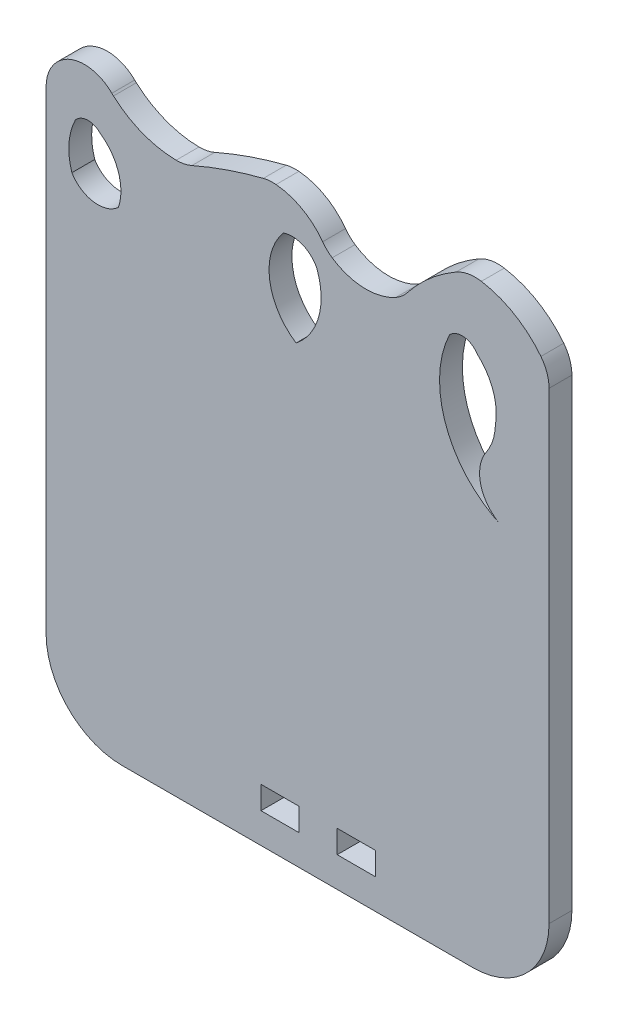
SolidWorks part; units mm, degrees
ref_plane "Alzado" through (0, 0, 0) normal (0, 0, 1) x (1, 0, 0)
ref_plane "Planta" through (0, 0, 0) normal (0, 1, 0) x (1, 0, 0)
ref_plane "Vista lateral" through (0, 0, 0) normal (1, 0, 0) x (0, 0, -1)
sketch "Model" plane through (0, 0, 0) normal (0, 0, 1) x (1, 0, 0)
  line L0 (38.1985, -8.9589) -> (43.1985, -8.9589)
  line L1 (43.1985, -8.9589) -> (43.1985, -5.9589)
  line L2 (43.1985, -5.9589) -> (38.1985, -5.9589)
  line L3 (38.1985, -5.9589) -> (38.1985, -8.9589)
  line L4 (48.1985, -8.9589) -> (53.1985, -8.9589)
  line L5 (53.1985, -8.9589) -> (53.1985, -5.9589)
  line L6 (53.1985, -5.9589) -> (48.1985, -5.9589)
  line L7 (48.1985, -5.9589) -> (48.1985, -8.9589)
  line L8 (20.0082, -12.9394) -> (66.0103, -12.8936)
  line L9 (75.9985, -2.8936) -> (75.9985, 57.9458)
  line L10 (9.9985, 59.261) -> (9.9985, 49.8017)
  line L11 (9.9985, 49.8017) -> (9.9985, 5.5632)
  line L12 (9.9985, 5.5632) -> (9.9985, -2.9394)
  arc A0 (9.9985, -2.9394) -> (20.0082, -12.9394) centre (19.9985, -2.9394) ccw
  arc A1 (66.0103, -12.8936) -> (75.9985, -2.8936) centre (65.9985, -2.8936) ccw
  arc A2 (75.9985, 57.9458) -> (74.9307, 61.0341) centre (70.9985, 57.9458) ccw
  arc A3 (74.9307, 61.0341) -> (67.1201, 65.6619) centre (65.0622, 53.2836) ccw
  arc A4 (67.1201, 65.6619) -> (63.7991, 65.0592) centre (66.3001, 60.7296) ccw
  arc A5 (63.7991, 65.0592) -> (57.3753, 59.4894) centre (75.0293, 45.6177) ccw
  arc A6 (55.9125, 58.2306) -> (57.3753, 59.4894) centre (53.4438, 62.5787) ccw
  arc A7 (47.5394, 58.5438) -> (55.9125, 58.2306) centre (51.9792, 65.1583) ccw
  arc A8 (46.2904, 59.7433) -> (47.5394, 58.5438) centre (50.3259, 62.6953) ccw
  arc A9 (46.2904, 59.7433) -> (40.1771, 63.1909) centre (39.4326, 54.7269) ccw
  arc A10 (40.1771, 63.1909) -> (38.5054, 63.0555) centre (39.739, 58.2101) ccw
  arc A11 (38.5054, 63.0555) -> (29.1327, 59.8249) centre (53.3214, 4.8609) ccw
  arc A12 (27.065, 59.4016) -> (29.1327, 59.8249) centre (27.1187, 64.4013) ccw
  arc A13 (18.8383, 62.586) -> (27.065, 59.4016) centre (27.2, 71.969) ccw
  arc A14 (18.6238, 62.7888) -> (18.8383, 62.586) centre (22.1648, 66.3188) ccw
  arc A15 (18.6238, 62.7888) -> (9.9985, 59.261) centre (15.0478, 59.2238) ccw
  arc A16 (13.3815, 51.1388) -> (19.4893, 50.2397) centre (16.8057, 53.2046) ccw
  arc A17 (19.4893, 50.2397) -> (17.071, 57.4946) centre (13.4428, 52.2547) ccw
  arc A18 (17.071, 57.4946) -> (13.8466, 57.3706) centre (15.5153, 55.9622) ccw
  arc A19 (13.8466, 57.3706) -> (13.3815, 51.1388) centre (21.2318, 53.6862) ccw
  arc A20 (42.8062, 46.4961) -> (45.513, 56.3753) centre (37.4749, 53.2673) ccw
  arc A21 (45.513, 56.3753) -> (41.152, 58.1677) centre (42.3026, 54.7656) ccw
  arc A22 (41.152, 58.1677) -> (42.8062, 46.4961) centre (47.0848, 53.0555) ccw
  arc A23 (67.7533, 46.5612) -> (69.9298, 39.1378) centre (71.882, 43.7409) ccw
  arc A24 (67.7533, 46.5612) -> (68.9587, 50.2574) centre (62.0254, 50.4738) ccw
  arc A25 (68.9587, 50.2574) -> (66.5671, 57.1235) centre (61.655, 51.563) ccw
  arc A26 (66.5671, 57.1235) -> (62.9412, 57.5093) centre (64.6033, 55.8988) ccw
  arc A27 (62.9412, 57.5093) -> (69.9298, 39.1378) centre (75.2471, 51.6755) ccw
extrude "Saliente-Extruir1" add sketch "Model" along normal blind 3
